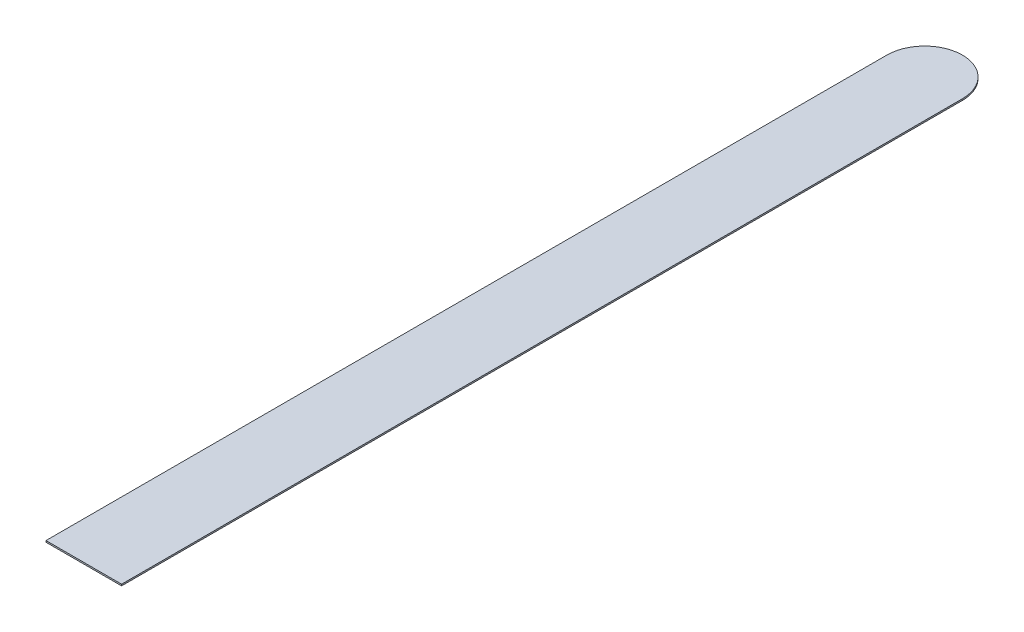
SolidWorks part; units mm, degrees
ref_plane "Front Plane" through (0, 0, 0) normal (0, 0, 1) x (1, 0, 0)
ref_plane "Top Plane" through (0, 0, 0) normal (0, 1, 0) x (1, 0, 0)
ref_plane "Right Plane" through (0, 0, 0) normal (1, 0, 0) x (0, 0, -1)
sketch "Sketch1" plane through (0, 0, 0) normal (0, 1, 0) x (1, 0, 0)
  line L0 (3.175, 73.8124) -> (3.175, 0) construction
  line L1 (0, 0) -> (6.35, 0)
  line L2 (0, 0) -> (0, 70.6374)
  line L4 (6.35, 0) -> (6.35, 70.6374)
  arc A0 (6.35, 70.6374) -> (0, 70.6374) centre (3.175, 70.6374) ccw
  dimension "D4" = 6.35
  dimension "D2" = 6.35
  dimension "D3" = 3.175
extrude "Boss-Extrude1" add sketch "Sketch1" along normal blind 0.127
